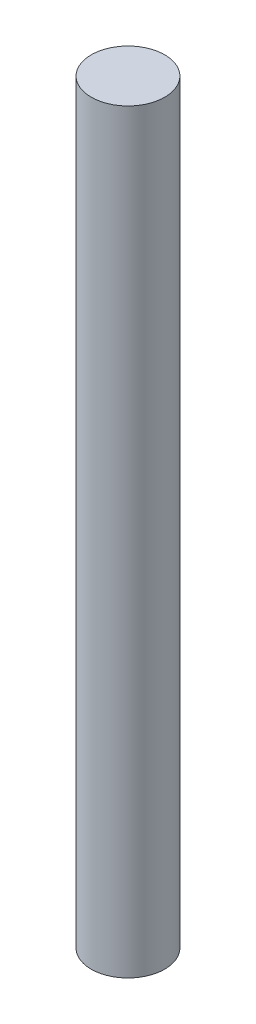
SolidWorks part; units mm, degrees
ref_plane "Front Plane" through (0, 0, 0) normal (0, 0, 1) x (1, 0, 0)
ref_plane "Top Plane" through (0, 0, 0) normal (0, 1, 0) x (1, 0, 0)
ref_plane "Right Plane" through (0, 0, 0) normal (1, 0, 0) x (0, 0, -1)
sketch "Sketch1" plane through (0, 0, 0) normal (0, 1, 0) x (1, 0, 0)
  circle A0 centre (0, 0) radius 914.4
  dimension "D1" = 1828.8
extrude "Boss-Extrude1" add sketch "Sketch1" along normal blind 18796
